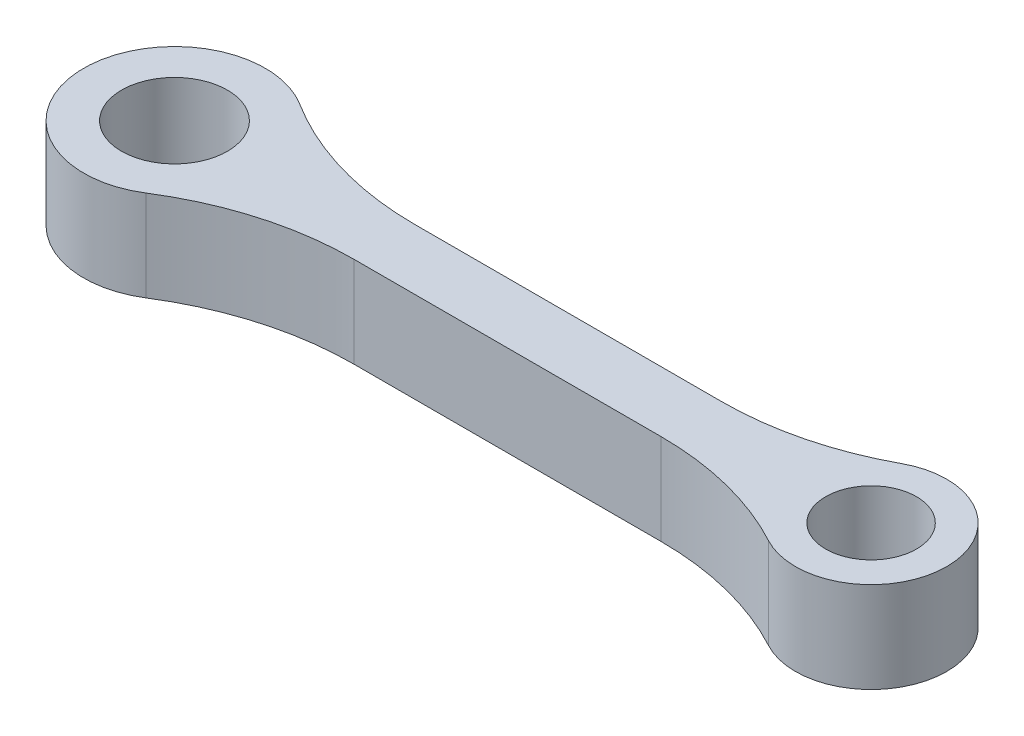
SolidWorks part; units mm, degrees
ref_plane "Front Plane" through (0, 0, 0) normal (0, 0, 1) x (1, 0, 0)
ref_plane "Top Plane" through (0, 0, 0) normal (0, 1, 0) x (1, 0, 0)
ref_plane "Right Plane" through (0, 0, 0) normal (1, 0, 0) x (0, 0, -1)
sketch "Sketch1" plane through (0, 0, 0) normal (0, 1, 0) x (1, 0, 0)
  line L1 (6.9282, 1) -> (17.0628, 1)
  line L3 (6.9282, -1) -> (17.0628, -1)
  circle A0 centre (0, 0) radius 1.75
  circle A1 centre (23, 0) radius 1.5
  arc A2 (1.5988, 2.5385) -> (1.5988, -2.5385) centre (0, 0) ccw
  arc A3 (21.8126, -2.2) -> (21.8126, 2.2) centre (23, 0) ccw
  arc A4 (6.9282, -1) -> (1.5988, -2.5385) centre (6.9282, -11) ccw
  arc A5 (17.0628, -1) -> (21.8126, -2.2) centre (17.0628, -11) cw
  arc A6 (17.0628, 1) -> (21.8126, 2.2) centre (17.0628, 11) ccw
  arc A7 (6.9282, 1) -> (1.5988, 2.5385) centre (6.9282, 11) cw
  dimension "D2" = 3.5
  dimension "D3" = 3
  dimension "D5" = 6
  dimension "D6" = 5
  dimension "D8" = 10
  dimension "D1" = 23
  dimension "D4" = 2
  dimension "D7" = 1
extrude "Boss-Extrude1" add sketch "Sketch1" along normal blind 3
